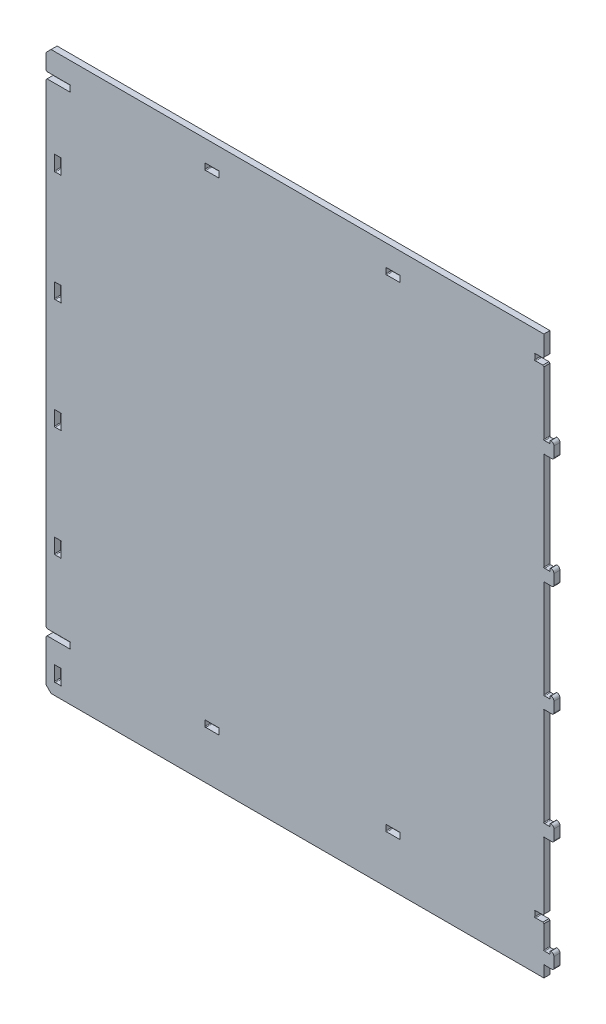
SolidWorks part; units mm, degrees
material "Acrylic (Medium-high impact)"
ref_plane "Front Plane" through (0, 0, 0) normal (0, 0, 1) x (1, 0, 0)
ref_plane "Top Plane" through (0, 0, 0) normal (0, 1, 0) x (1, 0, 0)
ref_plane "Right Plane" through (0, 0, 0) normal (1, 0, 0) x (0, 0, -1)
sketch "Sketch1" plane through (0, 0, 0) normal (0, 0, 1) x (1, 0, 0)
  line L0 (0, 555) -> (495.4, 555)
  line L1 (0, 555) -> (0, 0)
  line L2 (495.4, 555) -> (495.4, 0)
  line L3 (0, 0) -> (495.4, 0)
  dimension "D1" = 495.4
  dimension "D2" = 555
extrude "Boss-Extrude1" add sketch "Sketch1" along normal blind 6
sketch "Sketch3" plane through (0, 0, 6) normal (0, 0, 1) x (1, 0, 0)
  line L0 (495.4, 23.5001) -> (501.4, 23.5001)
  line L1 (495.4, 0) -> (495.4, 555) construction
  line L2 (501.4, 23.5001) -> (501.4, 25.5001)
  line L3 (503.4, 11.5) -> (495.4, 11.5)
  line L4 (495.4, 11.5) -> (495.4, 23.5001)
  line L5 (0, 0) -> (495.4, 0) construction
  line L6 (502.4, 26.5001) -> (502.4, 23.5001) construction
  line L7 (505.4, 23.5001) -> (505.4, 13.5)
  arc A0 (502.4, 26.5001) -> (505.4, 23.5001) centre (502.4, 23.5001) cw
  arc A1 (505.4, 13.5) -> (503.4, 11.5) centre (503.4, 13.5) cw
  arc A2 (501.4, 25.5001) -> (502.4, 26.5001) centre (502.4, 25.5001) cw
  dimension "D1" = 15.0001
  dimension "D3" = 6
  dimension "D4" = 2
  dimension "D5" = 1
  dimension "D6" = 3
  dimension "D2" = 4
  dimension "D7" = 11.5
extrude "Boss-Extrude2" add sketch "Sketch3" against normal up to surface (6 mm away) up to face at (247.7, 277.5, 0)
sketch "Sketch2" plane through (0, 0, 6) normal (0, 0, 1) x (1, 0, 0)
  line L0 (8.5, 11.5) -> (8.5, 26.5)
  line L1 (0, 555) -> (0, 0) construction
  line L3 (15, 26.5) -> (15, 11.5)
  line L4 (15, 11.5) -> (8.5, 11.5)
  line L5 (8.5, 26.5) -> (15, 26.5)
  line L6 (15, 19) -> (0, 19) construction
  line L7 (495.4, 11.5) -> (15, 11.5) construction
  dimension "D2" = 6.5
  dimension "D3" = 15
  dimension "D4" = 15
extrude "Cut-Extrude1" cut sketch "Sketch2" against normal through all
sketch "Sketch6" plane through (0, 0, 6) normal (0, 0, 1) x (1, 0, 0)
  line L0 (8.5, 12.2071) -> (8.5, 11.5) construction
  line L1 (8.5, 26.5) -> (8.5, 11.5) construction
  line L2 (8.5, 11.5) -> (9.2071, 11.5) construction
  line L3 (15, 26.5) -> (8.5, 26.5) construction
  line L4 (8.5, 25.7929) -> (8.5, 26.5) construction
  line L5 (14.2929, 11.5) -> (15, 11.5) construction
  line L6 (15, 11.5) -> (15, 12.2071) construction
  line L7 (15, 11.5) -> (15, 26.5) construction
  line L8 (8.5, 26.5) -> (9.2071, 26.5) construction
  line L10 (495.4, 24.2072) -> (495.4, 23.5001) construction
  line L11 (14.2929, 26.5) -> (15, 26.5) construction
  line L12 (15, 26.5) -> (15, 25.7929) construction
  line L13 (495.4, 23.5001) -> (495.4, 555) construction
  line L14 (495.4, 23.5001) -> (496.1071, 23.5001) construction
  line L15 (501.4, 23.5001) -> (495.4, 23.5001) construction
  line L16 (495.4, 11.5) -> (503.4, 11.5) construction
  line L17 (501.4, 24.2072) -> (501.4, 23.5001) construction
  line L18 (501.4, 25.5001) -> (501.4, 23.5001) construction
  line L19 (501.4, 23.5001) -> (500.6929, 23.5001) construction
  line L21 (496.1071, 11.5) -> (495.4, 11.5) construction
  line L22 (495.4, 11.5) -> (495.4, 10.7929) construction
  line L23 (495.4, 0) -> (495.4, 11.5) construction
  circle A0 centre (8.8536, 11.8536) radius 0.5
  circle A1 centre (14.6464, 11.8536) radius 0.5
  circle A2 centre (14.6464, 26.1464) radius 0.5
  circle A3 centre (8.8536, 26.1464) radius 0.5
  circle A4 centre (495.7536, 23.8536) radius 0.5
  circle A5 centre (501.0464, 23.8536) radius 0.5
  circle A6 centre (495.7536, 11.1464) radius 0.5
  dimension "D1" = 1
extrude "Cut-Extrude4" cut sketch "Sketch6" against normal through all
pattern_linear "LPattern1" count 5 spacing 110 along (0, 1, 0) of "Boss-Extrude2", "Cut-Extrude1", "Cut-Extrude4"
sketch "Sketch5" plane through (0, 0, 6) normal (0, 0, 1) x (1, 0, 0)
  line L0 (0, 555) -> (0, 0) construction
  line L1 (0, 47.7) -> (24, 47.7)
  line L2 (0, 47.7) -> (0, 53.9)
  line L3 (0, 53.9) -> (24, 53.9)
  line L4 (24, 47.7) -> (24, 53.9)
  line L5 (0, 0) -> (495.4, 0) construction
  line L6 (495.4, 23.5001) -> (495.4, 121.5) construction
  line L7 (486.4, 47.7) -> (495.4, 47.7)
  line L8 (486.4, 47.7) -> (486.4, 53.9)
  line L9 (486.4, 53.9) -> (495.4, 53.9)
  line L10 (495.4, 47.7) -> (495.4, 53.9)
  dimension "D1" = 6.2
  dimension "D2" = 24
  dimension "D3" = 9
  dimension "D4" = 47.7
extrude "Cut-Extrude3" cut sketch "Sketch5" against normal up to next (6 mm away)
sketch "Sketch7" plane through (0, 0, 6) normal (0, 0, 1) x (1, 0, 0)
  line L0 (23.2929, 47.7) -> (24, 47.7) construction
  line L1 (0, 47.7) -> (24, 47.7) construction
  line L2 (24, 47.7) -> (24, 48.4071) construction
  line L3 (24, 47.7) -> (24, 53.9) construction
  line L4 (486.4, 53.1929) -> (486.4, 53.9) construction
  line L5 (24, 53.1929) -> (24, 53.9) construction
  line L6 (24, 53.9) -> (23.2929, 53.9) construction
  line L7 (24, 53.9) -> (0, 53.9) construction
  line L8 (486.4, 53.9) -> (486.4, 47.7) construction
  line L9 (486.4, 53.9) -> (487.1071, 53.9) construction
  line L10 (495.4, 53.9) -> (486.4, 53.9) construction
  line L11 (486.4, 47.7) -> (495.4, 47.7) construction
  line L12 (486.4, 48.4071) -> (486.4, 47.7) construction
  line L13 (486.4, 47.7) -> (487.1071, 47.7) construction
  line L17 (24, 47.7) -> (24, 53.9) construction
  line L22 (0, 53.9) -> (24, 53.9) construction
  circle A0 centre (486.7536, 53.5464) radius 0.5
  circle A1 centre (486.7536, 48.0536) radius 0.5
  circle A2 centre (23.6464, 53.5464) radius 0.5
  circle A3 centre (23.6464, 48.0536) radius 0.5
  dimension "D1" = 1
extrude "Cut-Extrude5" cut sketch "Sketch7" against normal through all
sketch "Sketch8" plane through (0, 0, 6) normal (0, 0, 1) x (1, 0, 0)
  line L0 (345.2, 50.8) -> (165.2, 50.8) construction
  line L1 (158.2, 53.9) -> (172.2, 53.9)
  line L2 (158.2, 53.9) -> (158.2, 47.7)
  line L3 (158.2, 47.7) -> (172.2, 47.7)
  line L4 (172.2, 53.9) -> (172.2, 47.7)
  line L9 (255.2, 50.8) -> (255.2, 12.2071) construction
  line L10 (15, 12.2071) -> (495.4, 12.2071) construction
  line L11 (165.2, 47.7) -> (165.2, 53.9) construction
  line L13 (495.4, 0) -> (495.4, 10.7929) construction
  line L14 (0, 47.7) -> (24, 47.7) construction
  line L15 (0, 53.9) -> (24, 53.9) construction
  dimension "D1" = 14
  dimension "D2" = 180
extrude "Cut-Extrude6" cut sketch "Sketch8" against normal through all
sketch "Sketch9" plane through (0, 0, 6) normal (0, 0, 1) x (1, 0, 0)
  line L0 (158.2, 53.9) -> (158.2, 53.1929) construction
  line L1 (158.2, 53.9) -> (158.9071, 53.9) construction
  line L2 (172.2, 47.7) -> (172.2, 53.9) construction
  line L3 (171.4929, 53.9) -> (172.2, 53.9) construction
  line L4 (172.2, 53.9) -> (172.2, 53.1929) construction
  line L6 (172.2, 48.4071) -> (172.2, 47.7) construction
  line L7 (172.2, 47.7) -> (171.4929, 47.7) construction
  line L9 (158.9071, 47.7) -> (158.2, 47.7) construction
  line L10 (158.2, 47.7) -> (158.2, 48.4071) construction
  circle A0 centre (158.5536, 53.5464) radius 0.5
  circle A1 centre (158.5536, 48.0536) radius 0.5
  circle A2 centre (171.8464, 48.0536) radius 0.5
  circle A3 centre (171.8464, 53.5464) radius 0.5
  dimension "D1" = 1
extrude "Cut-Extrude7" cut sketch "Sketch9" against normal through all
pattern_linear "LPattern4" count 2 spacing 180 along (1, 0, 0) of "Cut-Extrude6", "Cut-Extrude7"
chamfer "Chamfer2" distance 1 angle 45 4 edges at (0, 53.9, 3) (0, 47.7, 3) (495.4, 53.9, 3) (495.4, 47.7, 3)
pattern_linear "LPattern3" count 2 spacing 480 along (0, 1, 0) of "Chamfer2", "Cut-Extrude3", "Cut-Extrude5", "LPattern4", "Cut-Extrude6", "Cut-Extrude7"
chamfer "Chamfer1" distance 5 angle 45 2 edges at (0, 0, 3) (0, 555, 3)
other "Save Bodies1"
